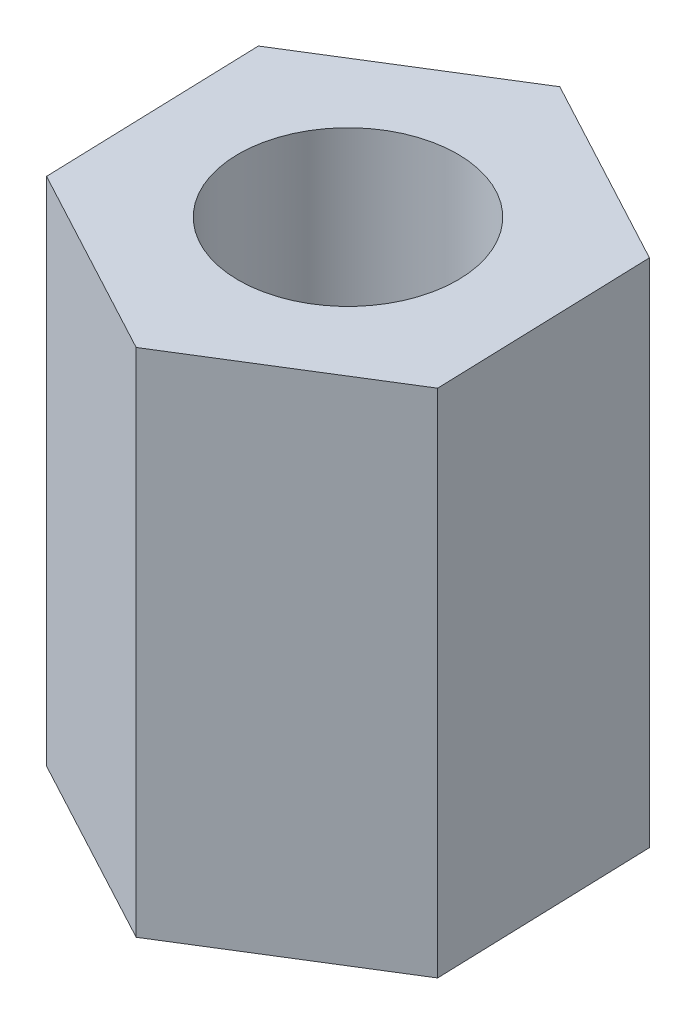
SolidWorks part; units mm, degrees
ref_plane "Front Plane" through (0, 0, 0) normal (0, 0, 1) x (1, 0, 0)
ref_plane "Top Plane" through (0, 0, 0) normal (0, 1, 0) x (1, 0, 0)
ref_plane "Right Plane" through (0, 0, 0) normal (1, 0, 0) x (0, 0, -1)
sketch "Sketch1" plane through (0, 0, 0) normal (0, 1, 0) x (1, 0, 0)
  line L1 (2.5489, 1.5821) -> (-0.0957, 2.9985)
  line L2 (-0.0957, 2.9985) -> (-2.6446, 1.4164)
  line L3 (-2.6446, 1.4164) -> (-2.5489, -1.5821)
  line L4 (-2.5489, -1.5821) -> (0.0957, -2.9985)
  line L5 (0.0957, -2.9985) -> (2.6446, -1.4164)
  line L6 (2.6446, -1.4164) -> (2.5489, 1.5821)
  circle A0 centre (0, 0) radius 1.5
  circle A1 centre (0, 0) radius 2.5981 construction
  circle A2 centre (0, 0) radius 3 construction
  dimension "D1" = 3
  dimension "D3" = 6
extrude "Boss-Extrude2" add sketch "Sketch1" along normal blind 7
equation "\"thread_dist\"= 3.5"
equation "\"thread_diameter\"= 3"
equation "\"D13@Sketch1\"=\"thread_diameter\""
equation "\"D14@Sketch1\"=\"thread_dist\""
equation "\"D11@Sketch1\"=\"thread_diameter\""
equation "\"D12@Sketch1\"=\"thread_dist\""
equation "\"D8@Sketch1\"=\"thread_diameter\""
equation "\"D10@Sketch1\"=\"thread_dist\""
equation "\"D1@Sketch1\"=\"thread_diameter\""
equation "\"thread_length\"=12"
equation "\"D1@Boss-Extrude1\"=\"thread_length\""
equation "\"D1@Boss-Extrude2\"=\"thread_length\"-5"
